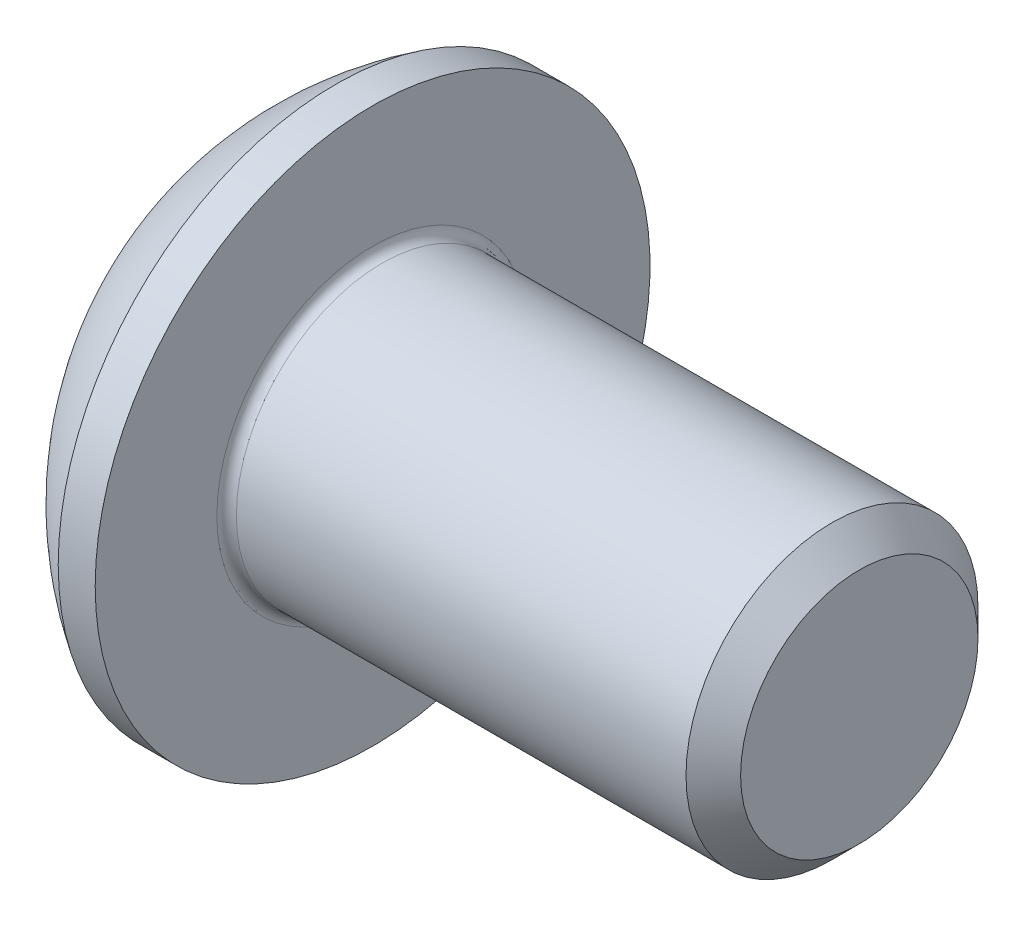
SolidWorks part; units mm, degrees
ref_plane "Plane1" through (0, 0, 0) normal (0, 0, 1) x (1, 0, 0)
ref_plane "Plane2" through (0, 0, 0) normal (0, 1, 0) x (1, 0, 0)
ref_plane "Plane3" through (0, 0, 0) normal (1, 0, 0) x (0, 0, -1)
other "Configuration Table"
sketch "BodySke" plane through (0, 0, 0) normal (0, 0, 1) x (1, 0, 0)
  line L0 (6.65, 0) -> (6.65, 1.2195)
  line L1 (6.3695, 1.5) -> (1.65, 1.5)
  line L2 (1.65, 1.5) -> (1.65, 2.85)
  line L3 (1.65, 2.85) -> (1.27, 2.85)
  line L4 (0, 0) -> (101.6, 0) construction
  line L5 (1.65, -2.85) -> (1.27, -2.85) construction
  line L6 (55.6768, -1.5) -> (1.65, -1.5) construction
  line L7 (6.65, 0) -> (0, 0)
  line L8 (0, 1.425) -> (0, -1.425) construction
  line L9 (0, 0) -> (0, 1.425)
  line L10 (6.65, 1.2195) -> (6.3695, 1.5)
  line L11 (6.65, -1.2195) -> (6.3695, -1.5) construction
  line L12 (2.15, 9.525) -> (2.15, -1.5) construction
  line L13 (1.65, 9.525) -> (1.65, -1.5) construction
  arc A1 (0, 1.425) -> (1.27, 2.85) centre (3.0334, 0) cw
  dimension "Diameter" = 3
  dimension "Length" = 5
  dimension "Head_dia" = 5.7
  dimension "D1" = 2.85
  dimension "Head_ht" = 1.65
  dimension "Head_side_ht" = 0.38
  dimension "Minor_dia" = 2.439
  dimension "Body_ch_ang" = 45
  dimension "Advance" = 0.5
  dimension "Thread_nom" = 5
revolve "BaseBody" add sketch "BodySke" angle 360 about L4
cosmetic thread "ThreadCosmetic" [suppressed] parameters "Thread_length"=4, "Thread_minor"=2.439
fillet "Fillet1" radius 0.1 1 edges at (1.65, 0, 1.5)
sketch "Sketch2" plane through (0, 0, 0) normal (0, 0, 1) x (1, 0, 0)
  line L0 (0, 1) -> (1.04, 1)
  line L1 (1.04, 1) -> (1.6174, 0)
  line L3 (1.6174, 0) -> (0, 0)
  line L4 (0, 0) -> (0, 1)
  line L5 (0, -1) -> (1.04, -1) construction
  line L6 (0, 0) -> (47.625, 0) construction
  dimension "D2" = 60
  dimension "PreBroach_depth" = 1.04
  dimension "PreBroach_dia" = 2
revolve "PreBroach" cut sketch "Sketch2" angle 360 about L6
sketch "Sketch3" plane through (0, 0, 0) normal (1, 0, 0) x (0, 0, -1)
  line L0 (-1, -0.5774) -> (-1, 0.5774)
  line L1 (-1, 0.5774) -> (0, 1.1547)
  line L2 (0, 1.1547) -> (1, 0.5774)
  line L3 (1, 0.5774) -> (1, -0.5774)
  line L4 (1, -0.5774) -> (0, -1.1547)
  line L5 (0, -1.1547) -> (-1, -0.5774)
  dimension "Hex_size" = 2
  dimension "D3" = 2
  dimension "D1" = 1
  dimension "D2" = 1
extrude "Hex" cut sketch "Sketch3" along normal blind 1.04
sketch "ThdSchSke" plane through (0, 0, 0) normal (0, 0, 1) x (1, 0, 0)
  line L0 (2.65, -1.2195) -> (2.4536, -1.5)
  line L1 (2.65, -1.2195) -> (2.8464, -1.5)
  line L2 (2.8464, -1.5) -> (2.8464, -1.875)
  line L3 (-3.175, 0) -> (5.1513, 0) construction
  line L5 (2.8464, -1.875) -> (2.4536, -1.875)
  line L6 (2.4536, -1.875) -> (2.4536, -1.5)
  dimension "Diameter" = 3
  dimension "Thread_minor" = 2.439
  dimension "SideAngle" = 55
  dimension "VeeAngle" = 70
  dimension "Overcut" = 3.75
  dimension "Start" = 2.65
revolve "ThreadSchematic" [suppressed] cut sketch "ThdSchSke" angle 360 about L3
pattern_linear "ThdSchPat" [suppressed]
equation "\"D1@BodySke\" = \"Head_dia@BodySke\" * .5"
equation "\"Thread_minor@ThreadCosmetic\" = \"Minor_dia@BodySke\""
equation "\"D1@Sketch3\" = \"Hex_size@Sketch3\" / 2"
equation "\"D2@Sketch3\" = \"D1@Sketch3\""
equation "\"D3@Sketch3\" = \"Hex_size@Sketch3\""
equation "\"Thread_length@ThreadCosmetic\" = ((sgn( (\"Length@BodySke\" - \"Advance@BodySke\" * 2.0) - \"Thread_nom@BodySke\" )-1)*( (\"Length@BodySke\" - \"Advance@BodySke\" * 2.0) - \"Thread_nom@BodySke\" ))/-2+ \"Thread_nom@BodySke\""
equation "\"Thread_minor@ThdSchSke\" = \"Minor_dia@BodySke\""
equation "\"Diameter@ThdSchSke\" = \"Diameter@BodySke\""
equation "\"Overcut@ThdSchSke\" = \"Diameter@BodySke\" * 1.25"
equation "\"Start@ThdSchSke\" = \"Head_ht@BodySke\" + \"Length@BodySke\" - \"Thread_length@ThreadCosmetic\"  '---Non-countersunk---"
equation "\"Num_threads@ThdSchPat\" = int( \"Thread_length@ThreadCosmetic\" / \"Advance@BodySke\" + 0.999 )  + 1"
equation "\"Advance@ThdSchPat\" = \"Thread_length@ThreadCosmetic\" /  (\"Num_threads@ThdSchPat\" - 1) 'relax it"
equation "\"Num_threads@ThdSchPat\" = \"Num_threads@ThdSchPat\" - sgn( \"Num_threads@ThdSchPat\" - 1) '---chamfered tips only---"
